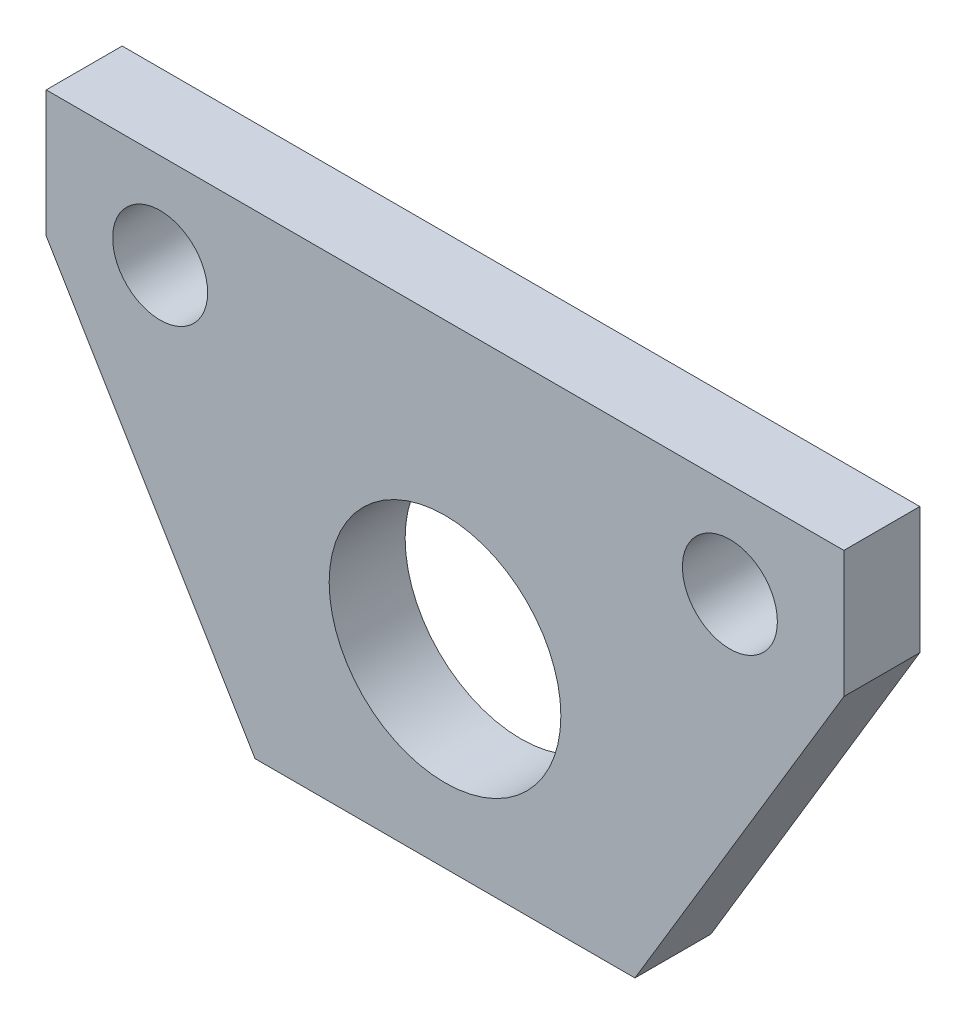
SolidWorks part; units mm, degrees
ref_plane "Front Plane" through (0, 0, 0) normal (0, 0, 1) x (1, 0, 0)
ref_plane "Top Plane" through (0, 0, 0) normal (0, 1, 0) x (1, 0, 0)
ref_plane "Right Plane" through (0, 0, 0) normal (1, 0, 0) x (0, 0, -1)
sketch "Sketch1" plane through (0, 0, 0) normal (0, 0, 1) x (1, 0, 0)
  line L0 (-31.75, 31.75) -> (31.75, 31.75)
  line L5 (31.75, 31.75) -> (12.7, 0)
  line L6 (-31.75, 31.75) -> (-12.7, 0)
  line L11 (-12.7, 0) -> (12.7, 0)
  point P4 (0, 31.75)
  point P6 (0, 0)
  dimension "D1" = 25.4
  dimension "D2" = 63.5
  dimension "D3" = 31.75
extrude "Boss-Extrude1" add sketch "Sketch1" along normal blind 5.08
sketch "Sketch3" plane through (0, 0, 5.08) normal (0, 0, 1) x (1, 0, 0)
  line L0 (-19.05, 25.4) -> (19.05, 25.4) construction
  line L1 (-26.67, 23.2833) -> (-26.67, 31.75)
  line L2 (-31.75, 31.75) -> (-12.7, 0) construction
  line L3 (-31.75, 31.75) -> (31.75, 31.75) construction
  line L4 (-26.67, 31.75) -> (-31.75, 31.75)
  line L5 (-31.75, 31.75) -> (-26.67, 23.2833)
  line L6 (26.67, 31.75) -> (26.67, 23.2833)
  line L7 (31.75, 31.75) -> (12.7, 0) construction
  line L8 (26.67, 23.2833) -> (31.75, 31.75)
  line L9 (31.75, 31.75) -> (26.67, 31.75)
  circle A0 centre (0, 12.7) radius 7.747
  circle A1 centre (-19.05, 25.4) radius 3.175
  circle A2 centre (19.05, 25.4) radius 3.175
  point P7 (0, 25.4)
  dimension "D1" = 15.494
  dimension "D3" = 6.35
  dimension "D2" = 12.7
  dimension "D4" = 12.7
  dimension "D5" = 38.1
  dimension "D6" = 7.62
extrude "Cut-Extrude2" cut sketch "Sketch3" against normal blind 5.08
